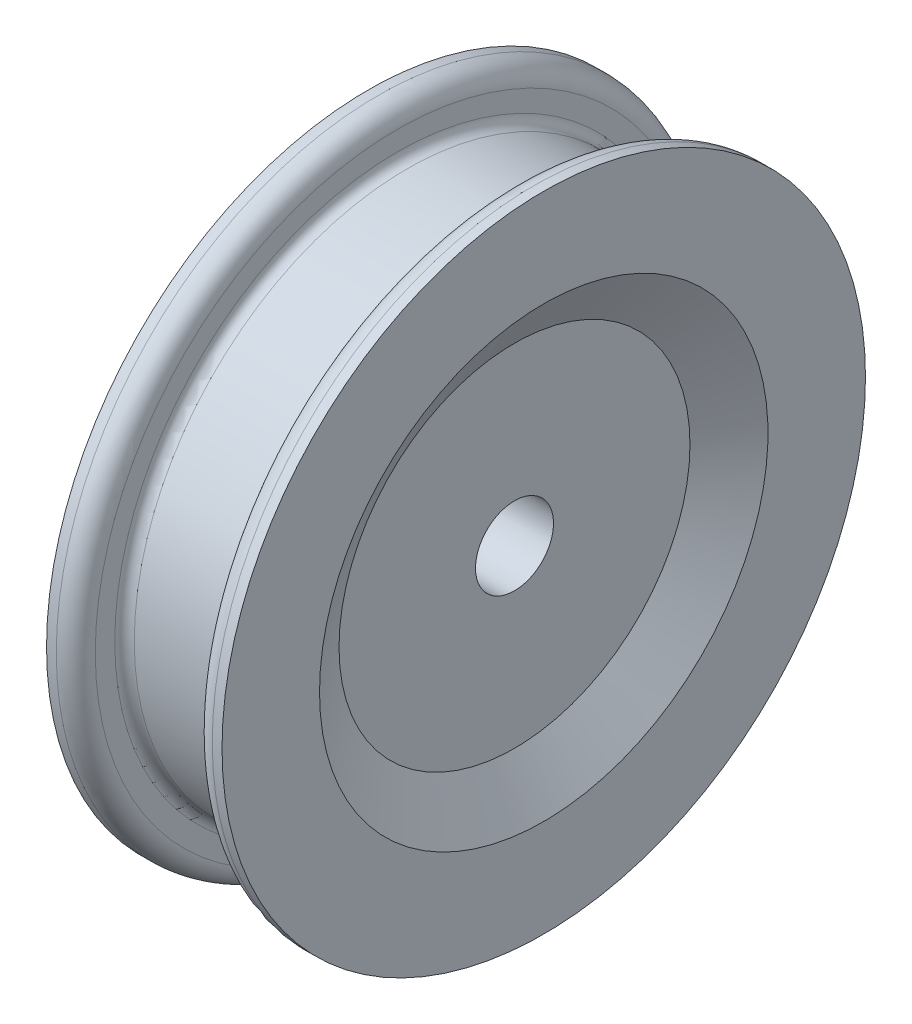
SolidWorks part; units mm, degrees
ref_plane "Front" through (0, 0, 0) normal (0, 0, 1) x (1, 0, 0)
ref_plane "Top" through (0, 0, 0) normal (0, 1, 0) x (1, 0, 0)
ref_plane "Right" through (0, 0, 0) normal (1, 0, 0) x (0, 0, -1)
sketch "Sketch1" plane through (0, 0, 0) normal (0, 0, 1) x (1, 0, 0)
  line L0 (-1.5, 1) -> (1.5, 1)
  line L2 (2.25, 8.25) -> (1.5, 8.25)
  line L3 (1.5, 8.25) -> (1.5, 7.25)
  line L4 (1.25, 7) -> (-1.25, 7)
  line L5 (0, 7) -> (0, 1) construction
  line L6 (0, 0) -> (4.984, 0) construction
  line L7 (-1.5, 8.25) -> (-1.5, 7.25)
  line L8 (-2.25, 8.25) -> (-1.5, 8.25)
  line L10 (2.25, 8.25) -> (2.25, 5.75)
  line L11 (2.25, 5.75) -> (1.5, 4.5)
  line L12 (1.5, 4.5) -> (1.5, 1)
  line L13 (-1.5, 4.5) -> (-1.5, 1)
  line L14 (-2.25, 5.75) -> (-1.5, 4.5)
  line L15 (-2.25, 8.25) -> (-2.25, 5.75)
  arc A0 (1.5, 7.25) -> (1.25, 7) centre (1.25, 7.25) cw
  arc A1 (-1.5, 7.25) -> (-1.25, 7) centre (-1.25, 7.25) ccw
  point P9 (0, 7)
  point P16 (1.5, 7)
  point P19 (-1.5, 7)
  dimension "D6" = 0.25
  dimension "D1" = 2
  dimension "D2" = 14
  dimension "D3" = 16.5
  dimension "D4" = 3
  dimension "D5" = 0.75
  dimension "D7" = 3.5
  dimension "D8" = 4.5
  dimension "D9" = 2.5
revolve "Revolve1" add sketch "Sketch1" angle 360 about L6
ref_point "Point1"
fillet "Fillet1" radius 0.5 2 edges at (-1.5, 0, 8.25) (1.5, 0, 8.25)
